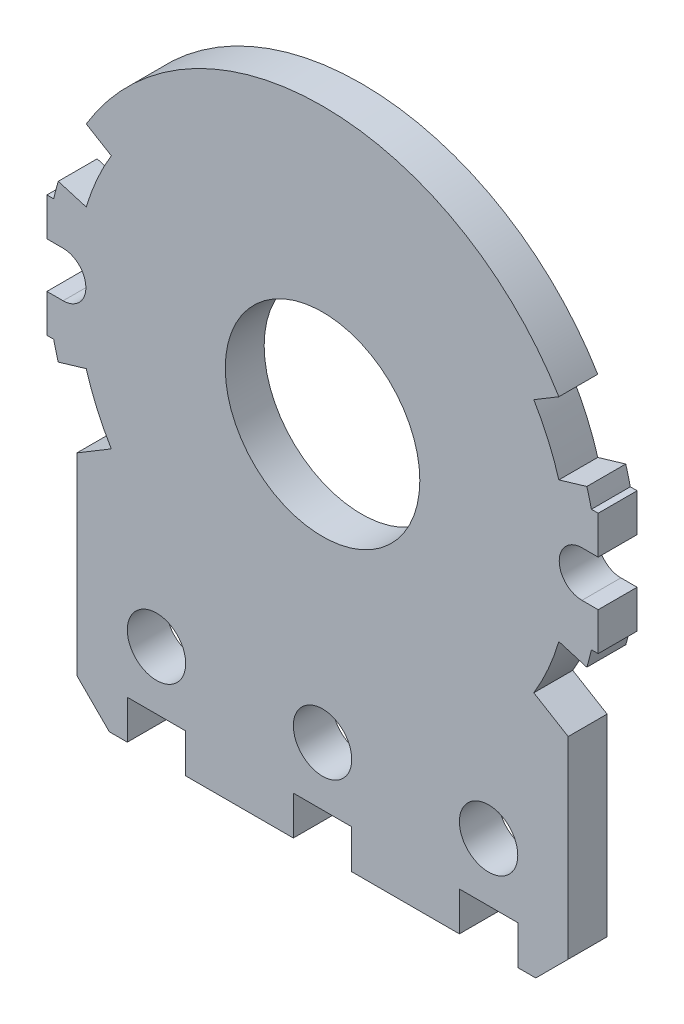
SolidWorks part; units mm, degrees
material "ABS"
ref_plane "Front" through (0, 0, 0) normal (0, 0, 1) x (1, 0, 0)
ref_plane "Top" through (0, 0, 0) normal (0, 1, 0) x (1, 0, 0)
ref_plane "Right" through (0, 0, 0) normal (1, 0, 0) x (0, 0, -1)
sketch "Sketch1" plane through (0, 0, 0) normal (0, 0, 1) x (1, 0, 0)
  line L0 (0, 0) -> (0, -7.678) construction
  line L1 (0, 8.5) -> (13.6887, 8.5) construction
  line L2 (-7.575, -11.5) -> (7.575, -11.5)
  line L3 (-7.575, -11.5) -> (-7.575, -3.8561)
  line L4 (-7.575, -3.8561) -> (7.575, -3.8561)
  line L5 (7.575, -11.5) -> (7.575, -3.8561)
  line L6 (-7.575, -11.5) -> (7.575, -3.8561) construction
  line L7 (-7.575, -3.8561) -> (7.575, -11.5) construction
  line L8 (13.6887, 8.5) -> (13.6887, -11.5) construction
  line L9 (13.6887, -11.5) -> (7.575, -11.5) construction
  line L11 (-8.5, -1.875) -> (8.5, -1.875)
  line L12 (-8.5, -1.875) -> (-8.5, 1.875)
  line L13 (-8.5, 1.875) -> (8.5, 1.875)
  line L14 (8.5, -1.875) -> (8.5, 1.875)
  line L15 (-8.5, -1.875) -> (8.5, 1.875) construction
  line L16 (-8.5, 1.875) -> (8.5, -1.875) construction
  circle A0 centre (0, 0) radius 8.5
  circle A1 centre (0, 0) radius 3
extrude "Boss-Extrude1" add sketch "Sketch1" along normal blind 1.2 contours A1 L4 A0 | A1 L4 A0 | A0 L3 L2 L5 | A1 L13 A0 L11 | A0 L12 L11 | A0 L13 L12 | A1 L13 A0 | A1 L11 A0 L13 | A0 L14 L13 | A0 L11 L14
sketch "Sketch2" plane through (0, 0, 1.2) normal (0, 0, 1) x (1, 0, 0)
  line L0 (0, 0) -> (0, -11.5) construction
  line L1 (-7.575, -11.5) -> (7.575, -11.5) construction
  line L2 (4.22, -10.3) -> (6.02, -10.3)
  line L3 (-0.9, -10.3) -> (0.9, -10.3)
  line L4 (-0.9, -10.3) -> (-0.9, -11.5)
  line L5 (-0.9, -11.5) -> (0.9, -11.5)
  line L6 (0.9, -10.3) -> (0.9, -11.5)
  line L7 (-0.9, -10.3) -> (0.9, -11.5) construction
  line L8 (-0.9, -11.5) -> (0.9, -10.3) construction
  line L9 (4.22, -10.3) -> (4.22, -11.5)
  line L10 (4.22, -11.5) -> (6.02, -11.5)
  line L11 (6.02, -10.3) -> (6.02, -11.5)
  line L12 (-6.02, -10.3) -> (-6.02, -11.5)
  line L13 (-4.22, -11.5) -> (-6.02, -11.5)
  line L14 (-4.22, -10.3) -> (-4.22, -11.5)
  line L15 (-4.22, -10.3) -> (-6.02, -10.3)
  line L16 (7.575, -11.5) -> (7.575, -10.5)
  line L17 (7.575, -11.5) -> (7.575, -3.8561) construction
  line L18 (7.575, -10.5) -> (6.575, -11.5)
  line L19 (6.575, -11.5) -> (7.575, -11.5)
  line L20 (6.02, -10.3) -> (7.575, -10.3) construction
  line L21 (-6.575, -11.5) -> (-7.575, -11.5)
  line L22 (-7.575, -10.5) -> (-6.575, -11.5)
  line L23 (-7.575, -11.5) -> (-7.575, -10.5)
  line L24 (2.6771, -11.5) -> (2.6771, -8.5) construction
  line L25 (2.6771, -8.5) -> (5.12, -8.5) construction
  circle A0 centre (0, -8.5) radius 0.9
  circle A1 centre (5.12, -8.5) radius 0.9
  circle A2 centre (-5.12, -8.5) radius 0.9
  circle A3 centre (0, 0) radius 7.6 construction
  point P5 (0, -10.9)
  dimension "D2" = 2
  dimension "D1" = 2
extrude "Cut-Extrude1" cut sketch "Sketch2" against normal through all
sketch "Sketch3" plane through (0, 0, 1.2) normal (0, 0, 1) x (1, 0, 0)
  line L0 (0, 0) -> (8.5, 0) construction
  line L1 (7.287, 2.1585) -> (9.1197, 2.7014)
  line L2 (0, 0) -> (6.5145, 3.9143) construction
  line L3 (6.5145, 3.9143) -> (8.0188, 4.8182)
  line L4 (8.0188, 4.8182) -> (9.1197, 2.7014)
  line L5 (8.0188, -4.8182) -> (9.1197, -2.7014)
  line L6 (6.5145, -3.9143) -> (8.0188, -4.8182)
  line L7 (7.287, -2.1585) -> (9.1197, -2.7014)
  line L8 (0, 8.5) -> (0, 0) construction
  line L9 (-7.287, -2.1585) -> (-9.1197, -2.7014)
  line L10 (-6.5145, -3.9143) -> (-8.0188, -4.8182)
  line L11 (-8.0188, -4.8182) -> (-9.1197, -2.7014)
  line L12 (-8.0188, 4.8182) -> (-9.1197, 2.7014)
  line L13 (-6.5145, 3.9143) -> (-8.0188, 4.8182)
  line L14 (-7.287, 2.1585) -> (-9.1197, 2.7014)
  line L15 (0, 0) -> (7.287, 2.1585) construction
  line L16 (-9, -0.7017) -> (-8, -0.7017)
  line L17 (-9, -0.7017) -> (-9, 0.7017)
  line L18 (-9, 0.7017) -> (-8, 0.7017)
  line L19 (-8, -0.7017) -> (-8, 0.7017)
  line L20 (-9, -0.7017) -> (-8, 0.7017) construction
  line L21 (-9, 0.7017) -> (-8, -0.7017) construction
  line L22 (9, -0.7017) -> (8, -0.7017)
  line L23 (9, -0.7017) -> (9, 0.7017)
  line L24 (9, 0.7017) -> (8, 0.7017)
  line L25 (8, -0.7017) -> (8, 0.7017)
  line L26 (9, -0.7017) -> (8, 0.7017) construction
  line L27 (9, 0.7017) -> (8, -0.7017) construction
  arc A0 (7.575, -3.8561) -> (8.2906, -1.875) centre (0, 0) ccw construction
  circle A1 centre (8, 0) radius 0.7017
  arc A2 (6.5145, 3.9143) -> (7.287, 2.1585) centre (0, 0) cw
  arc A3 (6.5145, -3.9143) -> (7.287, -2.1585) centre (0, 0) ccw
  arc A4 (-6.5145, -3.9143) -> (-7.287, -2.1585) centre (0, 0) cw
  arc A5 (-6.5145, 3.9143) -> (-7.287, 2.1585) centre (0, 0) ccw
  circle A6 centre (-8, 0) radius 0.7017
  point P26 (-8.5, 0)
  line M17 (7.575, -10.5) -> (7.575, -3.8561)
  arc M18 (7.575, -3.8561) -> (8.2906, -1.875) centre (0, 0) ccw
  line M19 (-7.575, -3.8561) -> (-7.575, -10.5)
extrude "Cut-Extrude2" cut sketch "Sketch3" against normal blind 10 contours L25 A1 | A1 L25 M18 | A1 L24 M18 | A1 L22 M18 | A1 L22 L23 L24 M18 | A1 M18 | A6 L19 M18 | A6 M18 | A6 L18 L17 L16 M18 | A6 L18 M18 | L16 A6 M18 | A6 L19 | A5 L13 L14 M18 | L10 A4 L9 M18 M19 | L11 L10 L9 M19 M18 | L14 L13 L12 M18 | L7 L6 L5 M18 M17 | A3 L6 L7 M17 M18 | L4 L3 L1 M18 | L3 A2 L1 M18
